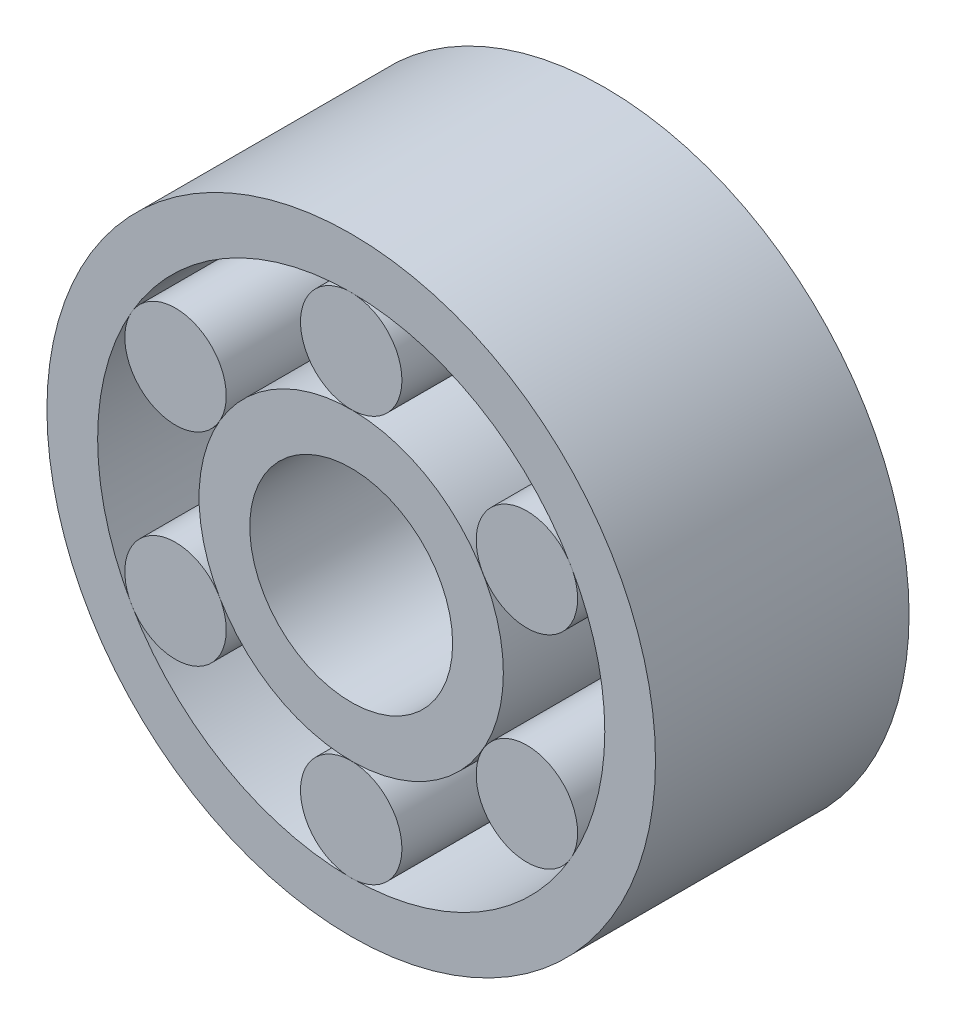
SolidWorks part; units mm, degrees
ref_plane "前视基准面" through (0, 0, 0) normal (0, 0, 1) x (1, 0, 0)
ref_plane "上视基准面" through (0, 0, 0) normal (0, 1, 0) x (1, 0, 0)
ref_plane "右视基准面" through (0, 0, 0) normal (1, 0, 0) x (0, 0, -1)
sketch "草图1" plane through (0, 0, 0) normal (0, 0, 1) x (1, 0, 0)
  circle A0 centre (0, 0) radius 1
  circle A1 centre (0, 0) radius 1.5
  circle A2 centre (0, 0) radius 3
  circle A3 centre (0, 0) radius 2.5
  circle A4 centre (0, 2) radius 0.5
  circle A5 centre (1.7321, 1) radius 0.5
  circle A6 centre (1.7321, -1) radius 0.5
  circle A7 centre (0, -2) radius 0.5
  circle A8 centre (-1.7321, -1) radius 0.5
  circle A9 centre (-1.7321, 1) radius 0.5
  point P21 (0, 0)
  dimension "D1" = 2
  dimension "D2" = 3
  dimension "D3" = 6
  dimension "D4" = 5
  dimension "D5" = 6
extrude "凸台-拉伸1" add sketch "草图1" along normal blind 2.5 contours A1 A0 | A4 | A2 A3 | A9 | A5 | A6 | A7 | A8
